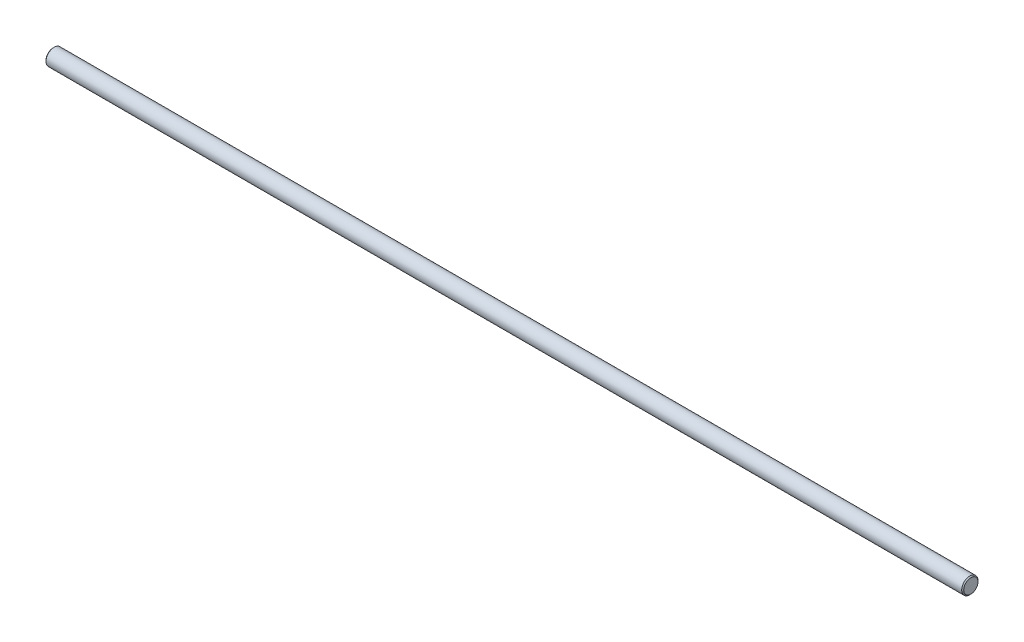
SolidWorks part; units mm, degrees
ref_plane "Front Plane" through (0, 0, 0) normal (0, 0, 1) x (1, 0, 0)
ref_plane "Top Plane" through (0, 0, 0) normal (0, 1, 0) x (1, 0, 0)
ref_plane "Right Plane" through (0, 0, 0) normal (1, 0, 0) x (0, 0, -1)
sketch "Sketch1" plane through (0, 0, 0) normal (1, 0, 0) x (0, 0, -1)
  circle A0 centre (0, 0) radius 4
  dimension "D1" = 8
extrude "Boss-Extrude1" add sketch "Sketch1" along normal blind 450
chamfer "Chamfer1" distance 0.5 angle 45 2 edges at (450, 0, -4) (0, 0, -4)
